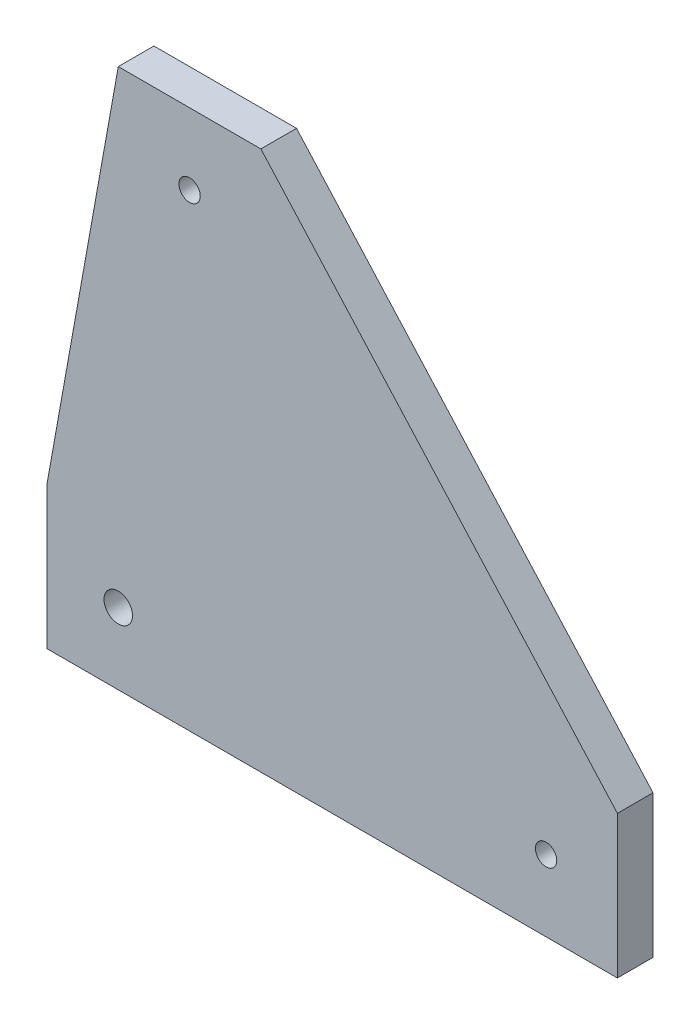
SolidWorks part; units mm, degrees
ref_plane "Front Plane" through (0, 0, 0) normal (0, 0, 1) x (1, 0, 0)
ref_plane "Top Plane" through (0, 0, 0) normal (0, 1, 0) x (1, 0, 0)
ref_plane "Right Plane" through (0, 0, 0) normal (1, 0, 0) x (0, 0, -1)
sketch "Sketch1" plane through (0, 0, 0) normal (0, 0, 1) x (1, 0, 0)
  line L0 (-26.9154, 0) -> (33.0846, 0) construction
  line L1 (-16.9154, 55.7063) -> (-16.9154, 0) construction
  line L2 (33.0846, 0) -> (43.0846, 0) construction
  line L3 (33.0846, 0) -> (33.0846, -10) construction
  line L4 (-26.9154, 0) -> (-36.9154, 0) construction
  line L5 (-26.9154, 0) -> (-26.9154, -10) construction
  line L6 (-16.9154, 55.7063) -> (-16.9154, 65.7063) construction
  line L7 (-16.9154, 55.7063) -> (-26.9154, 55.7063) construction
  line L8 (-26.9154, 65.7063) -> (-6.9154, 65.7063)
  line L9 (43.0846, -10) -> (43.0846, 10)
  line L10 (-36.9154, -10) -> (-36.9154, 10)
  line L11 (-36.9154, -10) -> (43.0846, -10)
  line L12 (-36.9154, 10) -> (-26.9154, 65.7063)
  line L13 (-6.9154, 65.7063) -> (43.0846, 10)
  circle A0 centre (-26.9154, 0) radius 2
  circle A1 centre (33.0846, 0) radius 1.5
  circle A2 centre (-16.9154, 55.7063) radius 1.5
  dimension "D2" = 55.7063
  dimension "D4" = 10
  dimension "D13" = 3
  dimension "D14" = 3
  dimension "D15" = 4
  dimension "D1" = 60
  dimension "D3" = 10
  dimension "D5" = 10
  dimension "D6" = 10
  dimension "D7" = 10
  dimension "D8" = 10
  dimension "D9" = 10
  dimension "D10" = 20
  dimension "D11" = 20
  dimension "D12" = 20
extrude "Boss-Extrude1" add sketch "Sketch1" along normal blind 5
